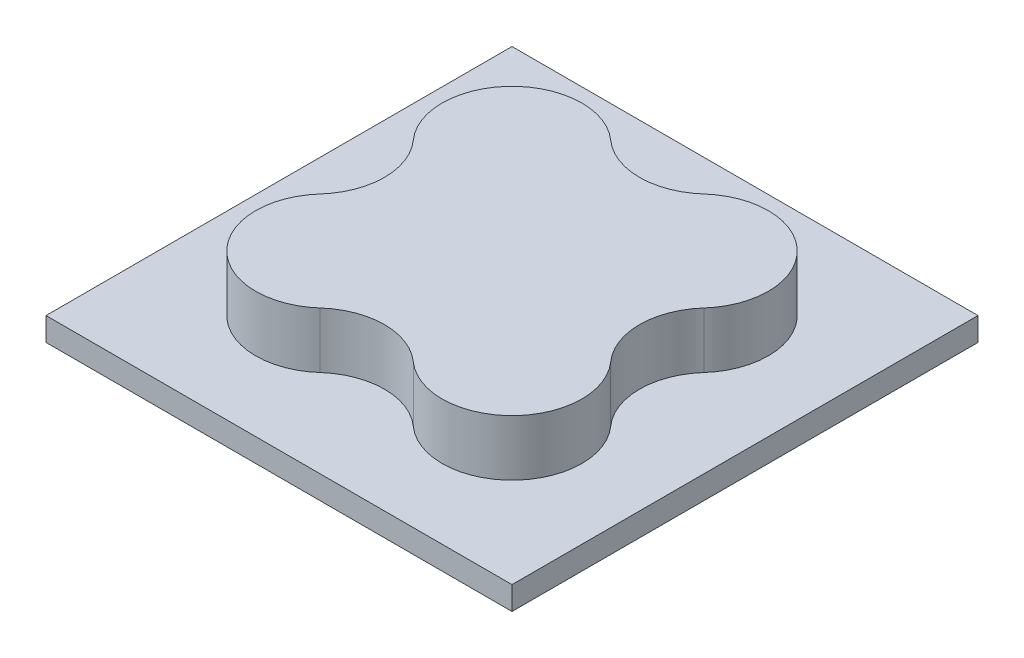
SolidWorks part; units mm, degrees
material "Alumina"
ref_plane "Front Plane" through (0, 0, 0) normal (0, 0, 1) x (1, 0, 0)
ref_plane "Top Plane" through (0, 0, 0) normal (0, 1, 0) x (1, 0, 0)
ref_plane "Right Plane" through (0, 0, 0) normal (1, 0, 0) x (0, 0, -1)
sketch "Sketch5" plane through (0, 0, 0) normal (0, 1, 0) x (1, 0, 0)
  line L1 (0, 0) -> (100, 0)
  line L2 (0, 0) -> (0, 100)
  line L3 (0, 100) -> (100, 100)
  line L4 (100, 0) -> (100, 100)
  dimension "D1" = 100
  dimension "D2" = 100
extrude "Boss-Extrude1" add sketch "Sketch5" along normal blind 5
sketch "Sketch7" plane through (0, 5, 0) normal (0, 1, 0) x (1, 0, 0)
  line L0 (-24.7424, 50) -> (131.7151, 50) construction
  line L1 (50, 122.4622) -> (50, -13.3553) construction
  line L2 (0, 100) -> (0, 0) construction
  line L3 (100, 0) -> (100, 100) construction
  line L4 (0, 0) -> (100, 0) construction
  line L5 (100, 100) -> (0, 100) construction
  arc A0 (81.1803, 60) -> (60, 81.1803) centre (70, 70) ccw
  arc A1 (40, 81.1803) -> (60, 81.1803) centre (50, 92.3607) ccw
  arc A2 (81.1803, 60) -> (81.1803, 40) centre (92.3607, 50) ccw
  arc A3 (60, 18.8197) -> (81.1803, 40) centre (70, 30) ccw
  arc A4 (60, 18.8197) -> (40, 18.8197) centre (50, 7.6393) ccw
  arc A5 (18.8197, 40) -> (40, 18.8197) centre (30, 30) ccw
  arc A6 (18.8197, 40) -> (18.8197, 60) centre (7.6393, 50) ccw
  arc A7 (40, 81.1803) -> (18.8197, 60) centre (30, 70) ccw
  dimension "D1" = 30
  dimension "D2" = 30
  dimension "D3" = 30
  dimension "D4" = 30
  dimension "D5" = 30
  dimension "D6" = 30
  dimension "D7" = 30
  dimension "D8" = 30
  dimension "D9" = 20
  dimension "D10" = 20
extrude "Boss-Extrude2" add sketch "Sketch7" along normal blind 12
